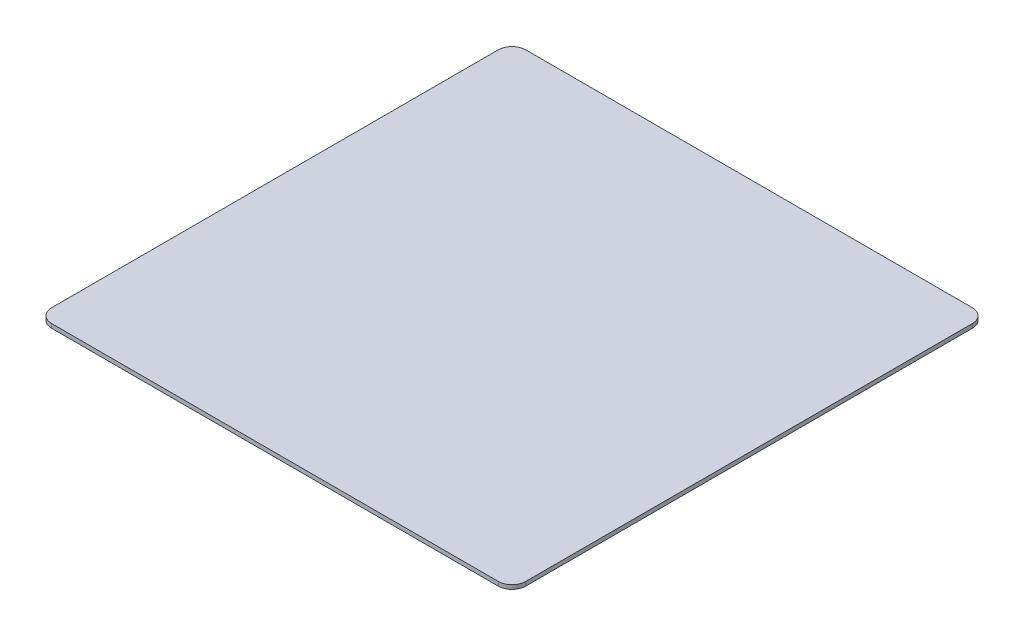
SolidWorks part; units mm, degrees
ref_plane "Front Plane" through (0, 0, 0) normal (0, 0, 1) x (1, 0, 0)
ref_plane "Top Plane" through (0, 0, 0) normal (0, 1, 0) x (1, 0, 0)
ref_plane "Right Plane" through (0, 0, 0) normal (1, 0, 0) x (0, 0, -1)
sketch "Sketch1" plane through (0, 0, 0) normal (0, 1, 0) x (1, 0, 0)
  line L1 (-32.5, -34.5) -> (32.5, -34.5)
  line L2 (-34.5, -32.5) -> (-34.5, 32.5)
  line L3 (-32.5, 34.5) -> (32.5, 34.5)
  line L4 (34.5, -32.5) -> (34.5, 32.5)
  line L5 (-34.5, -34.5) -> (34.5, 34.5) construction
  line L6 (-34.5, 34.5) -> (34.5, -34.5) construction
  arc A0 (-32.5, -34.5) -> (-34.5, -32.5) centre (-32.5, -32.5) cw
  arc A1 (32.5, -34.5) -> (34.5, -32.5) centre (32.5, -32.5) ccw
  arc A2 (32.5, 34.5) -> (34.5, 32.5) centre (32.5, 32.5) cw
  arc A3 (-34.5, 32.5) -> (-32.5, 34.5) centre (-32.5, 32.5) cw
  point P0 (0, 0)
  dimension "D2" = 2
  dimension "D1" = 69
extrude "Boss-Extrude1" add sketch "Sketch1" along normal blind 0.6
